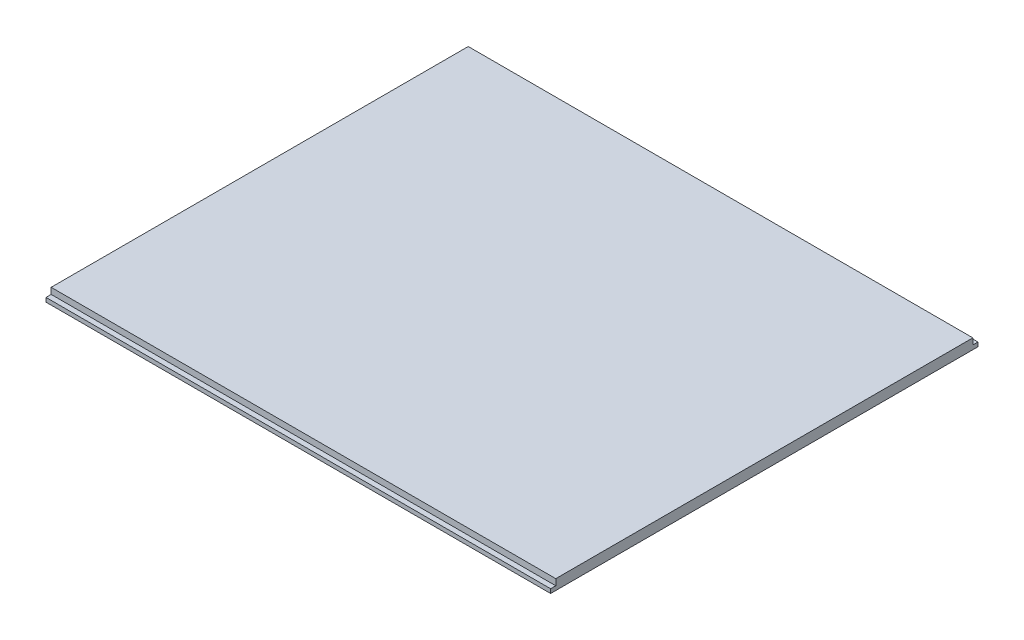
SolidWorks part; units mm, degrees
ref_plane "Front Plane" through (0, 0, 0) normal (0, 0, 1) x (1, 0, 0)
ref_plane "Top Plane" through (0, 0, 0) normal (0, 1, 0) x (1, 0, 0)
ref_plane "Right Plane" through (0, 0, 0) normal (1, 0, 0) x (0, 0, -1)
sketch "Sketch2" plane through (0, 0, 0) normal (0, 1, 0) x (1, 0, 0)
  line L1 (0, 0) -> (98, 0)
  line L2 (0, 0) -> (0, 83)
  line L3 (0, 83) -> (98, 83)
  line L4 (98, 0) -> (98, 83)
  dimension "D1" = 98
  dimension "D2" = 83
extrude "Boss-Extrude1" add sketch "Sketch2" along normal blind 2
sketch "Sketch3" plane through (0, 2, 0) normal (0, 1, 0) x (1, 0, 0)
  line L0 (98, 0) -> (98, 83) construction
  line L1 (0, 0) -> (98, 0)
  line L2 (0, 0) -> (0, 1)
  line L3 (0, 1) -> (98, 1)
  line L4 (98, 0) -> (98, 1)
  line L6 (0, 83) -> (98, 83)
  line L7 (0, 83) -> (0, 82)
  line L8 (0, 82) -> (98, 82)
  line L9 (98, 83) -> (98, 82)
  dimension "D1" = 1
  dimension "D2" = 1
extrude "Cut-Extrude1" cut sketch "Sketch3" against normal blind 1.2
